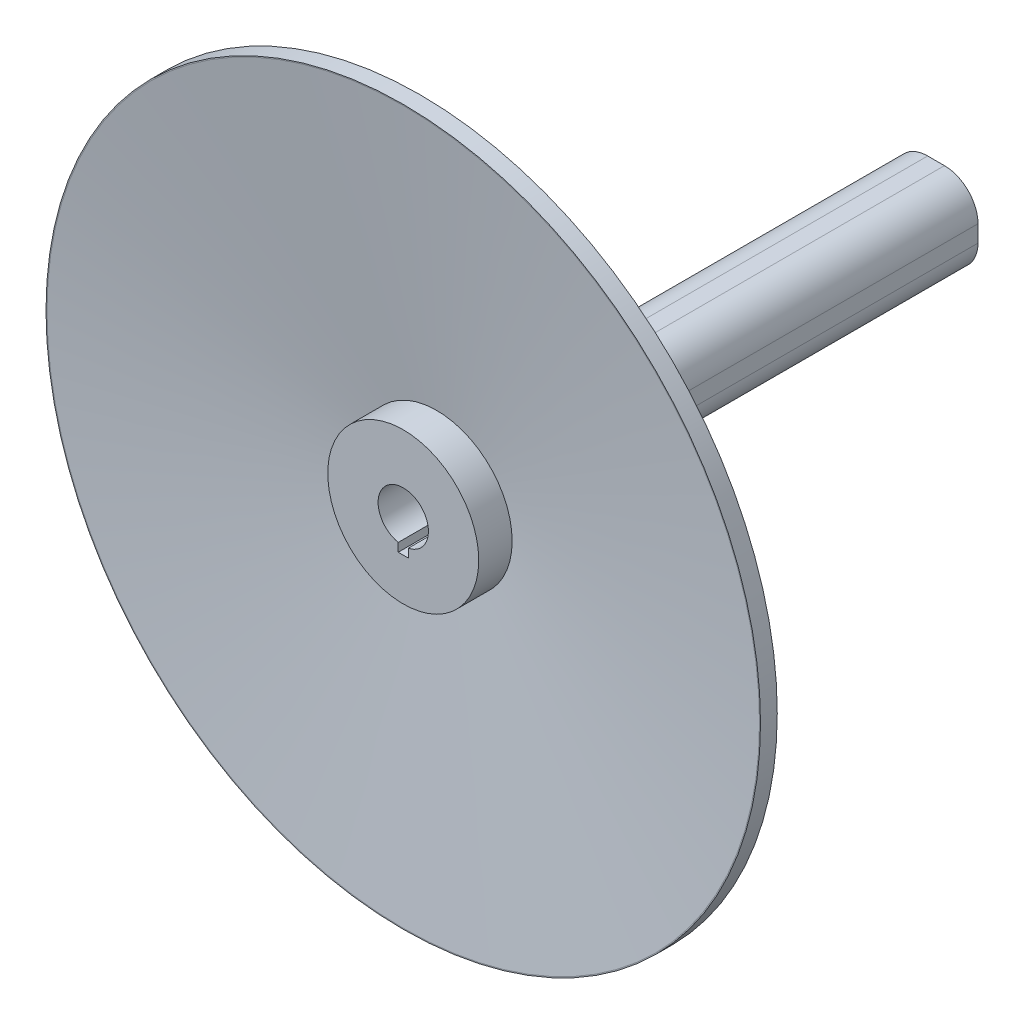
SolidWorks part; units mm, degrees
material "7075-T6 (SN)"
ref_plane "Front Plane" through (0, 0, 0) normal (0, 0, 1) x (1, 0, 0)
ref_plane "Top Plane" through (0, 0, 0) normal (0, 1, 0) x (1, 0, 0)
ref_plane "Right Plane" through (0, 0, 0) normal (1, 0, 0) x (0, 0, -1)
sketch "Sketch1" plane through (0, 0, 0) normal (0, 0, 1) x (1, 0, 0)
  circle A0 centre (0, 0) radius 22.5
  dimension "D1" = 45
extrude "Boss-Extrude1" add sketch "Sketch1" along normal blind 60
sketch "Sketch4" plane through (0, 0, 0) normal (0, 0, -1) x (-1, 0, 0)
  line L1 (-2.5, 12.5) -> (2.5, 12.5)
  line L2 (-12.5, 2.5) -> (-12.5, -2.5)
  line L3 (-2.5, -12.5) -> (2.5, -12.5)
  line L4 (12.5, 2.5) -> (12.5, -2.5)
  line L5 (-12.5, 12.5) -> (12.5, -12.5) construction
  line L6 (-12.5, -12.5) -> (12.5, 12.5) construction
  arc A0 (-12.5, -2.5) -> (-2.5, -12.5) centre (-2.5, -2.5) ccw
  arc A1 (2.5, -12.5) -> (12.5, -2.5) centre (2.5, -2.5) ccw
  arc A2 (2.5, 12.5) -> (12.5, 2.5) centre (2.5, 2.5) cw
  arc A3 (-2.5, 12.5) -> (-12.5, 2.5) centre (-2.5, 2.5) ccw
  point P0 (0, 0)
  dimension "D3" = 10
  dimension "D1" = 25
  dimension "D2" = 25
extrude "Boss-Extrude2" add sketch "Sketch4" along normal blind 98.8363
sketch "Sketch5" plane through (0, 0, 0) normal (1, 0, 0) x (0, 0, -1)
  line L0 (-60, 106.2034) -> (-60, 106.5)
  line L1 (-60, 106.5) -> (-55, 106.5)
  line L2 (-55, 106.5) -> (-45, 22.5)
  line L3 (0, 22.5) -> (-60, 22.5) construction
  line L4 (-45, 22.5) -> (-60, 22.5)
  line L5 (-60, 106.2034) -> (-50.0353, 22.5)
  line L6 (-59.9649, 105.9089) -> (-49.9649, 21.9089) construction
  dimension "D1" = 15
  dimension "D2" = 5
  dimension "D3" = 106.5
  dimension "D4" = 5
ref_axis "Axis1" through (0, 0, 60) along (0, 0, -1)
revolve "Revolve1" add sketch "Sketch5" angle 360 about axis through (0, 0, 60) along (0, 0, -1)
sketch "Sketch6" plane through (0, 0, -98.8363) normal (0, 0, -1) x (-1, 0, 0)
  circle A0 centre (0, 0) radius 7.5
  dimension "D1" = 15
extrude "Cut-Extrude1" cut sketch "Sketch6" against normal through all
sketch "Sketch7" plane through (0, 0, 60) normal (0, 0, 1) x (1, 0, 0)
  line L0 (0, -7.6033) -> (0, 0) construction
  line L1 (-1.5, -5.3198) -> (1.5, -5.3198)
  line L2 (-1.5, -5.3198) -> (-1.5, -9.8869)
  line L3 (-1.5, -9.8869) -> (1.5, -9.8869)
  line L4 (1.5, -5.3198) -> (1.5, -9.8869)
  line L5 (-1.5, -5.3198) -> (1.5, -9.8869) construction
  line L6 (-1.5, -9.8869) -> (1.5, -5.3198) construction
  circle A0 centre (0, 0) radius 10
  circle A1 centre (0, 0) radius 7.5 construction
  circle A2 centre (0, 0) radius 7.5
  point P6 (0, -7.6033)
  circle M4 centre (0, 0) radius 7.5
  dimension "D1" = 2.5
  dimension "D2" = 3
extrude "Cut-Extrude2" cut sketch "Sketch7" against normal blind 50 contours L4 L2 L3 M4
